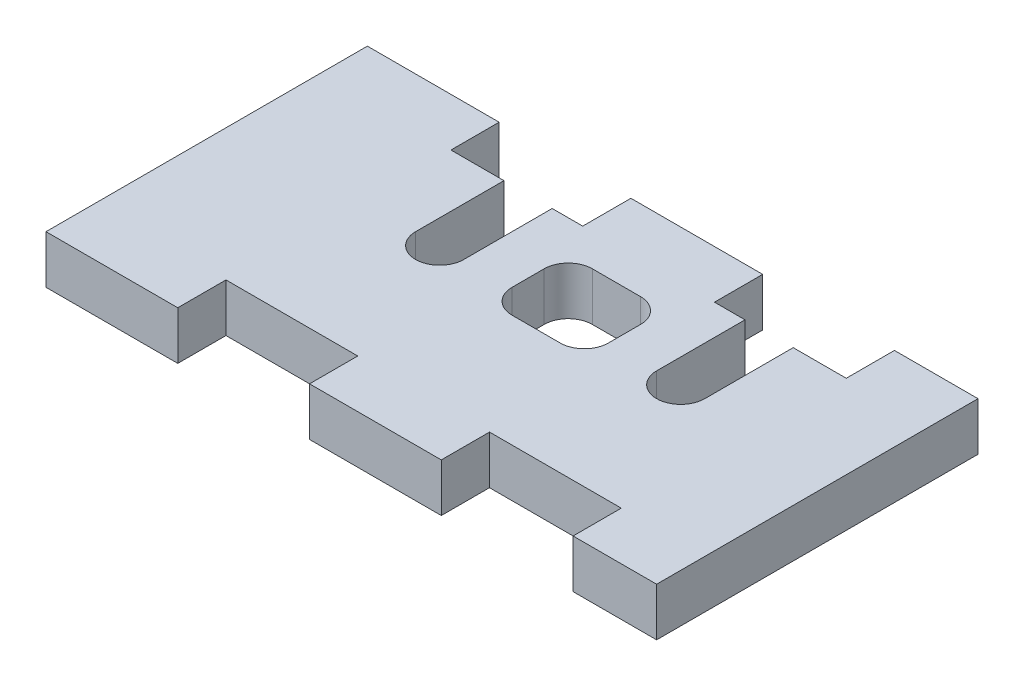
SolidWorks part; units mm, degrees
ref_plane "Front" through (0, 0, 0) normal (0, 0, 1) x (1, 0, 0)
ref_plane "Top" through (0, 0, 0) normal (0, 1, 0) x (1, 0, 0)
ref_plane "Right" through (0, 0, 0) normal (1, 0, 0) x (0, 0, -1)
sketch "Skizze1" plane through (0, 0, 0) normal (0, 1, 0) x (1, 0, 0)
  line L5 (0, 0) -> (38, 0) construction
  line L6 (0, 0) -> (0, 20) construction
  line L7 (0, 20) -> (38, 20) construction
  line L8 (38, 0) -> (38, 20) construction
  line L84 (0, 0) -> (8.1994, 0)
  line L85 (8.1994, 3.0002) -> (8.1994, 0)
  line L86 (8.1994, 3.0002) -> (16.4003, 3.0002)
  line L87 (16.4003, 3.0002) -> (16.4003, 0)
  line L88 (16.4003, 0) -> (24.5996, 0)
  line L89 (24.5996, 3.0002) -> (24.5996, 0)
  line L90 (24.5996, 3.0002) -> (32.8003, 3.0002)
  line L91 (32.8003, 3.0002) -> (32.8003, 0)
  line L92 (32.8003, 0) -> (37.9994, 0)
  line L93 (0, 20) -> (8.1994, 20)
  line L94 (8.1994, 20) -> (8.1994, 17)
  line L95 (8.1994, 17) -> (16.4003, 17)
  line L96 (16.4003, 20) -> (16.4003, 17)
  line L97 (16.4003, 20) -> (24.5996, 20)
  line L98 (24.5996, 20) -> (24.5996, 17)
  line L99 (24.5996, 17) -> (32.8003, 17)
  line L100 (32.8003, 20) -> (32.8003, 17)
  line L101 (32.8003, 20) -> (37.9994, 20)
  line L102 (0, 0) -> (0, 20)
  line L103 (37.9994, 0) -> (37.9994, 20)
  dimension "D1" = 20
  dimension "D2" = 38
  dimension "D3" = 3
extrude "Aufsatz-Linear austragen1" add sketch "Skizze1" along normal blind 3
sketch "Skizze2" plane through (0, 0, 0) normal (0, -1, 0) x (1, 0, 0)
  line L0 (13, -20) -> (13, -11.5) construction
  line L1 (11.5, -20) -> (11.5, -11.5)
  line L2 (14.5, -20) -> (14.5, -11.5)
  line L3 (20.5, -40) -> (20.5, 0) construction
  line L4 (24.5996, -20) -> (16.4003, -20) construction
  line L5 (16.4003, 0) -> (24.5996, 0) construction
  line L6 (11.5, -20) -> (14.5, -20)
  line L7 (26.5, -20) -> (29.5, -20)
  line L10 (28, -20) -> (28, -11.5) construction
  line L11 (29.5, -20) -> (29.5, -11.5)
  line L12 (26.5, -20) -> (26.5, -11.5)
  line L13 (9, -10) -> (12, -10) construction
  line L14 (8.1994, -20) -> (0, -20) construction
  line L15 (19, -10) -> (22, -10)
  line L16 (17.5, -13.5) -> (17.5, -11.5)
  line L17 (23.5, -13.5) -> (23.5, -11.5)
  line L18 (19, -15) -> (22, -15)
  line L19 (16.4003, -17) -> (8.1994, -17) construction
  arc A1 (14.5, -11.5) -> (11.5, -11.5) centre (13, -11.5) ccw
  arc A3 (26.5, -11.5) -> (29.5, -11.5) centre (28, -11.5) cw
  arc A5 (19, -10) -> (17.5, -11.5) centre (19, -11.5) ccw
  arc A6 (22, -10) -> (23.5, -11.5) centre (22, -11.5) cw
  arc A7 (23.5, -13.5) -> (22, -15) centre (22, -13.5) cw
  arc A8 (19, -15) -> (17.5, -13.5) centre (19, -13.5) cw
  point P10 (20.5, -20)
  dimension "D3" = 10
  dimension "D6" = 1.5
  dimension "D8" = 1.5
  dimension "D1" = 3
  dimension "D2" = 15
  dimension "D4" = 3
  dimension "D5" = 6
  dimension "D7" = 2
extrude "Schnitt-Linear austragen1" cut sketch "Skizze2" against normal up to next
